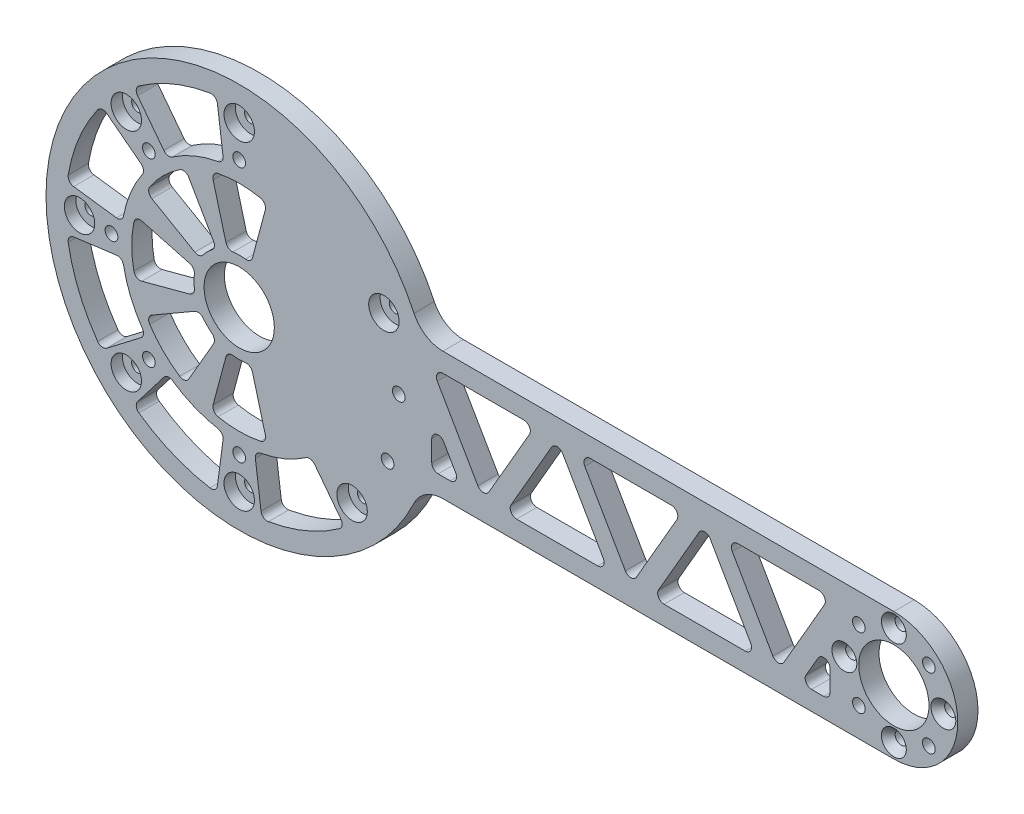
SolidWorks part; units mm, degrees
material "Balsa"
ref_plane "Front Plane" through (0, 0, 0) normal (0, 0, 1) x (1, 0, 0)
ref_plane "Top Plane" through (0, 0, 0) normal (0, 1, 0) x (1, 0, 0)
ref_plane "Right Plane" through (0, 0, 0) normal (1, 0, 0) x (0, 0, -1)
sketch "Sketch1" plane through (0, 0, 0) normal (0, 0, 1) x (1, 0, 0)
  line L0 (57.0986, -20) -> (205, -20)
  line L1 (57.0986, 20) -> (205, 20)
  line L2 (45.3154, 21.1309) -> (0, 0) construction
  line L3 (0, 0) -> (35.3553, -35.3553) construction
  line L4 (49.9788, 1.4542) -> (0, 0) construction
  line L5 (0, 0) -> (46.4674, -18.4603) construction
  arc A0 (57.0986, -20) -> (57.0986, 20) centre (0, 0) cw
  arc A1 (205, 20) -> (205, -20) centre (205, 0) cw
  circle A2 centre (0, 0) radius 60.5 construction
  circle A3 centre (0, 0) radius 11
  circle A4 centre (45.3154, 21.1309) radius 1.8986
  circle A5 centre (0, 0) radius 40 construction
  circle A6 centre (0, 0) radius 50 construction
  circle A7 centre (49.9788, 1.4542) radius 1.9939
  circle A8 centre (205, 0) radius 11
  circle A9 centre (46.4674, -18.4603) radius 1.9939
  circle A10 centre (205, 0) radius 15.5 construction
  circle A11 centre (205, -15.5) radius 1.8987
  circle A12 centre (215.9602, -10.9602) radius 1.9939
  circle A13 centre (189.5, 0) radius 1.8987
  circle A14 centre (194.0398, -10.9602) radius 1.9939
  circle A15 centre (205, 15.5) radius 1.8987
  circle A16 centre (194.0398, 10.9602) radius 1.9939
  circle A17 centre (220.5, 0) radius 1.8987
  circle A18 centre (215.9602, 10.9602) radius 1.9939
  circle A29 centre (0, -40) radius 1.9939
  circle A30 centre (0, -50) radius 1.8986
  circle A37 centre (-28.2843, -28.2843) radius 1.9939
  circle A38 centre (-35.3553, -35.3553) radius 1.8986
  circle A39 centre (-40, 0) radius 1.9939
  circle A40 centre (-50, 0) radius 1.8986
  circle A41 centre (-28.2843, 28.2843) radius 1.9939
  circle A42 centre (-35.3553, 35.3553) radius 1.8986
  circle A43 centre (0, 40) radius 1.9939
  circle A44 centre (0, 50) radius 1.8986
  circle A45 centre (28.2843, 28.2843) radius 1.9939 construction
  circle A46 centre (35.3553, 35.3553) radius 1.8986 construction
  circle A47 centre (40, 0) radius 1.9939 construction
  circle A48 centre (50, 0) radius 1.8986 construction
  circle A49 centre (28.2843, -28.2843) radius 1.9939 construction
  circle A50 centre (35.3553, -35.3553) radius 1.8986
  dimension "D1" = 121
  dimension "D4" = 22
  dimension "D6" = 100
  dimension "D7" = 80
  dimension "D8" = 70
  dimension "D9" = 3.7973
  dimension "D10" = 3.9878
  dimension "D15" = 3.7973
  dimension "D16" = 3.9878
  dimension "D17" = 3.7973
  dimension "D18" = 3.9878
  dimension "D5" = 31
  dimension "D19" = 3.9878
  dimension "D2" = 40
  dimension "D3" = 205
  dimension "D11" = 45
  dimension "D13" = 23.333
  dimension "D14" = 23.333
  dimension "D12" = 4
  dimension "D21" = 8
extrude "Boss-Extrude1" add sketch "Sketch1" along normal blind 6.35
fillet "Fillet1" radius 10 2 edges at (57.0986, -20, 3.175) (57.0986, 20, 3.175)
sketch "Sketch2" plane through (0, 0, 6.35) normal (0, 0, 1) x (1, 0, 0)
  line L0 (60.2923, 14) -> (92.624, 14)
  line L1 (92.624, 14) -> (76.4581, -14)
  line L2 (76.4581, -14) -> (60.2923, 14)
  line L3 (83.3864, -14) -> (99.5522, 14)
  line L4 (99.5522, 14) -> (115.718, -14)
  line L5 (115.718, -14) -> (83.3864, -14)
  line L6 (106.4804, 14) -> (122.6462, -14)
  line L7 (122.6462, -14) -> (138.812, 14)
  line L8 (138.812, 14) -> (106.4804, 14)
  line L9 (129.5744, -14) -> (145.7402, 14)
  line L10 (145.7402, 14) -> (161.906, -14)
  line L11 (161.906, -14) -> (129.5744, -14)
  line L12 (152.6684, 14) -> (168.8342, -14)
  line L13 (168.8342, -14) -> (185, 14)
  line L14 (185, 14) -> (152.6684, 14)
  line L15 (60.2923, 2) -> (60.2923, -14)
  line L16 (60.2923, -14) -> (69.5299, -14)
  line L17 (69.5299, -14) -> (60.2923, 2)
  line L18 (185, 2) -> (185, -14)
  line L19 (185, -14) -> (175.7624, -14)
  line L20 (175.7624, -14) -> (185, 2)
  line L21 (205, 20) -> (63.7985, 20) construction
  line L22 (63.7985, -20) -> (205, -20) construction
  arc A0 (205, -20) -> (205, 20) centre (205, 0) ccw construction
  point P25 (225, 0)
  dimension "D1" = 60
  dimension "D2" = 60
  dimension "D3" = 6
  dimension "D4" = 6
  dimension "D5" = 6
  dimension "D6" = 6
  dimension "D7" = 6
  dimension "D8" = 6
  dimension "D9" = 6
  dimension "D10" = 6
  dimension "D11" = 40
extrude "Cut-Extrude1" cut sketch "Sketch2" against normal through all
fillet "Fillet2" radius 2 21 edges at (175.7624, -14, 3.175) (69.5299, -14, 3.175) (129.5744, -14, 3.175) (83.3864, -14, 3.175) (122.6462, -14, 3.175) (76.4581, -14, 3.175) (60.2923, -14, 3.175) (60.2923, 2, 3.175) (99.5522, 14, 3.175) (145.7402, 14, 3.175) (185, 2, 3.175) (115.718, -14, 3.175) (161.906, -14, 3.175) (185, -14, 3.175) (168.8342, -14, 3.175) (185, 14, 3.175) (138.812, 14, 3.175) (92.624, 14, 3.175) (152.6684, 14, 3.175) (106.4804, 14, 3.175) (60.2923, 14, 3.175)
other "Move Face1" [suppressed] parameters "D1"=0.08
sketch "Sketch3" plane through (0, 0, 6.35) normal (0, 0, 1) x (1, 0, 0)
  line L0 (0, 0) -> (-71.2971, 0) construction
  line L1 (-32.5034, 8.7093) -> (-13.692, 3.6688)
  line L2 (-13.692, -3.6688) -> (-32.5034, -8.7093)
  arc A0 (-13.692, -3.6688) -> (-13.692, 3.6688) centre (0, 0) cw
  arc A1 (-32.5034, -8.7093) -> (-32.5034, 8.7093) centre (0, 0) cw
  circle A2 centre (0, 0) radius 11 construction
  circle A3 centre (-40, 0) radius 1.9939 construction
  point P7 (-14.175, 0)
  point P10 (-33.65, 0)
  dimension "D2" = 3.175
  dimension "D3" = 6.35
  dimension "D1" = 30
extrude "Cut-Extrude2" cut sketch "Sketch3" against normal through all
fillet "Fillet3" radius 2 4 edges at (-32.5034, -8.7093, 3.175) (-13.692, -3.6688, 3.175) (-13.692, 3.6688, 3.175) (-32.5034, 8.7093, 3.175)
pattern_circular "CirPattern1" count 8 over 360 about axis through (0, 0, 0) along (0, 0, 1) skipping 3, 4, 5 of "Fillet3", "Cut-Extrude2"
sketch "Sketch5" plane through (0, 0, 6.35) normal (0, 0, 1) x (1, 0, 0)
  line L0 (-78.0787, 0) -> (0, 0) construction
  line L1 (0, 0) -> (-81.1598, 33.6175) construction
  line L2 (-53.8602, 7.0908) -> (-36.51, 4.8066)
  line L3 (-43.0989, 33.071) -> (-29.2152, 22.4176)
  arc A0 (-36.51, 4.8066) -> (-29.2152, 22.4176) centre (0, 0) cw
  arc A1 (-53.8602, 7.0908) -> (-43.0989, 33.071) centre (0, 0) cw
  circle A2 centre (-35.3553, 35.3553) radius 1.8987 construction
  circle A3 centre (-28.2843, 28.2843) radius 1.9939 construction
  circle A4 centre (-35.3553, 35.3553) radius 1.8986 construction
  circle A5 centre (-28.2843, 28.2843) radius 1.9939 construction
  arc A6 (54.7491, 25.7447) -> (54.7491, -25.7447) centre (0, 0) ccw construction
  arc A7 (-32.9888, 6.6379) -> (-32.9888, -6.6379) centre (0, 0) ccw construction
  point P8 (-34.0219, 14.0923)
  dimension "D3" = 6.175
  dimension "D4" = 3.175
  dimension "D1" = 22.5
  dimension "D2" = 30
extrude "Cut-Extrude4" cut sketch "Sketch5" against normal through all
fillet "Fillet5" radius 2 4 edges at (-53.8602, 7.0908, 3.175) (-36.51, 4.8066, 3.175) (-29.2152, 22.4176, 3.175) (-43.0989, 33.071, 3.175)
pattern_circular "CirPattern3" count 8 over 360 about axis through (0, 0, 0) along (0, 0, 1) skipping 2, 3, 4 of "Fillet5", "Cut-Extrude4"
chamfer "Chamfer1" distance 2.301 angle 41 4 edges at (222.3986, 0, 6.35) (206.8987, -15.5, 6.35) (191.3987, 0, 6.35) (206.8987, 15.5, 6.35)
sketch "Sketch6" plane through (0, 0, 6.35) normal (0, 0, 1) x (1, 0, 0)
  circle A0 centre (45.3154, 21.1309) radius 1.8987 construction
  circle A1 centre (35.3553, -35.3553) radius 1.8987 construction
  circle A2 centre (0, -50) radius 1.8986 construction
  circle A3 centre (-35.3553, -35.3553) radius 1.8987 construction
  circle A4 centre (-50, 0) radius 1.8987 construction
  circle A5 centre (-35.3553, 35.3553) radius 1.8987 construction
  circle A6 centre (0, 50) radius 1.8986 construction
  circle A7 centre (45.3154, 21.1309) radius 1.8986
  circle A8 centre (35.3553, -35.3553) radius 1.8986
  circle A9 centre (0, -50) radius 1.8986
  circle A10 centre (-35.3553, -35.3553) radius 1.8986
  circle A11 centre (-50, 0) radius 1.8986
  circle A12 centre (-35.3553, 35.3553) radius 1.8986
  circle A13 centre (0, 50) radius 1.8986
  circle A14 centre (0, 50) radius 4.7625
  circle A15 centre (-35.3553, 35.3553) radius 4.7625
  circle A16 centre (-50, 0) radius 4.7625
  circle A17 centre (-35.3553, -35.3553) radius 4.7625
  circle A18 centre (0, -50) radius 4.7625
  circle A19 centre (35.3553, -35.3553) radius 4.7625
  circle A20 centre (45.3154, 21.1309) radius 4.7625
  dimension "D1" = 9.525
extrude "Cut-Extrude5" cut sketch "Sketch6" against normal blind 3.5719
